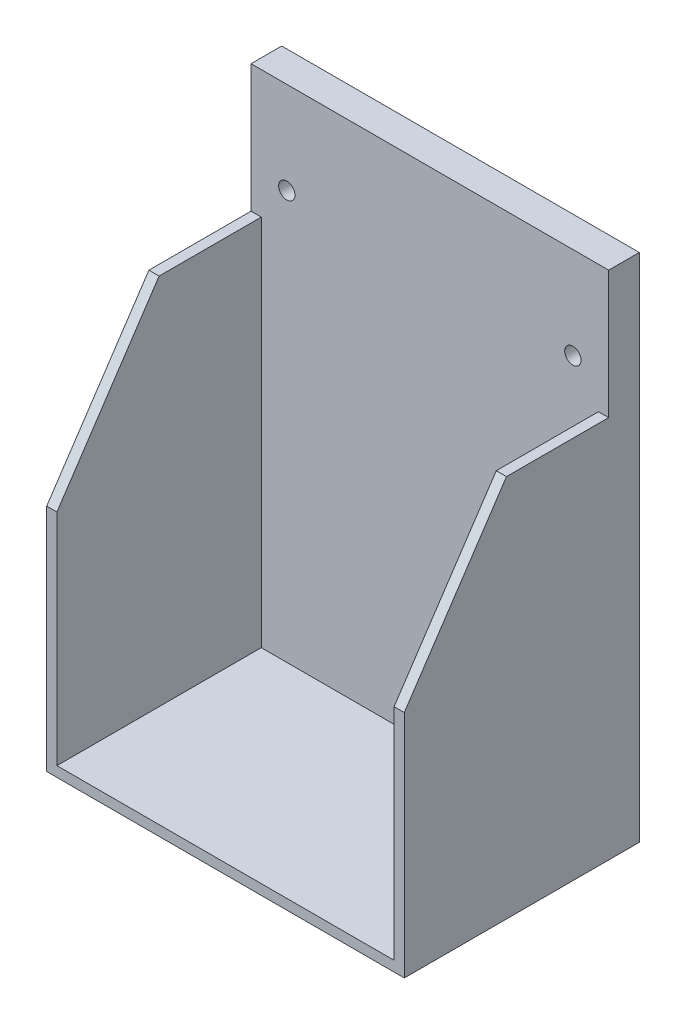
SolidWorks part; units mm, degrees
ref_plane "前视基准面" through (0, 0, 0) normal (0, 0, 1) x (1, 0, 0)
ref_plane "上视基准面" through (0, 0, 0) normal (0, 1, 0) x (1, 0, 0)
ref_plane "右视基准面" through (0, 0, 0) normal (1, 0, 0) x (0, 0, -1)
sketch "草图1" plane through (0, 0, 0) normal (0, 0, 1) x (1, 0, 0)
  line L0 (-21, -7.141) -> (49, -7.141) construction
  line L1 (-21, 17.859) -> (49, 17.859)
  line L2 (-21, 17.859) -> (-21, -82.141)
  line L3 (-21, -82.141) -> (49, -82.141)
  line L4 (49, 17.859) -> (49, -82.141)
  line L5 (-14, 17.859) -> (-14, -7.141) construction
  line L6 (-21, -0.141) -> (-14, -0.141) construction
  line L7 (14, 17.859) -> (14, -7.141) construction
  circle A0 centre (-14, -0.141) radius 1.6
  circle A1 centre (42, -0.141) radius 1.6
  dimension "D6" = 3.2
  dimension "D1" = 70
  dimension "D2" = 100
  dimension "D3" = 25
  dimension "D4" = 7
  dimension "D5" = 7
extrude "凸台-拉伸1" add sketch "草图1" along normal blind 6
sketch "草图2" plane through (0, 0, 6) normal (0, 0, 1) x (1, 0, 0)
  line L0 (-21, -82.141) -> (49, -82.141) construction
  line L1 (-21, -7.141) -> (-19, -7.141)
  line L2 (-21, -7.141) -> (-21, -82.141)
  line L3 (-21, -82.141) -> (-18.0557, -82.141)
  line L4 (-19, -7.141) -> (-19, -80.141)
  line L6 (49, -7.141) -> (47, -7.141)
  line L7 (49, -7.141) -> (49, -82.141)
  line L8 (49, -82.141) -> (46.0149, -82.141)
  line L9 (47, -7.141) -> (47, -80.141)
  line L10 (-19, -80.141) -> (47, -80.141)
  line L11 (-21, -80.141) -> (-21, -82.141)
  line L12 (-21, -82.141) -> (49, -82.141)
  line L13 (49, -79.478) -> (49, -82.141)
  point P16 (-19.8201, -82.141)
  point P17 (0, 0)
  point P18 (-18.0557, -82.141)
  point P19 (-21, -80.141)
  point P20 (0, 0)
  line M9 (-21, 17.859) -> (-21, -82.141)
  line M10 (-21, -82.141) -> (49, -82.141)
  line M11 (49, -82.141) -> (49, 17.859)
  dimension "D1" = 2
  dimension "D2" = 2
  dimension "D3" = 2
extrude "凸台-拉伸2" add sketch "草图2" along normal blind 40 contours L10 L4 L1 L2 L7 L6 L9 M9 M10 M11
sketch "草图3" plane through (-21, 0, 0) normal (-1, 0, 0) x (0, 0, 1)
  line L0 (26, -7.141) -> (46, -37.141)
  line L1 (46, -7.141) -> (6, -7.141) construction
  line L2 (46, -7.141) -> (46, -82.141) construction
  line L3 (46, -37.141) -> (46, -7.141)
  line L4 (46, -7.141) -> (26, -7.141)
  dimension "D1" = 20
  dimension "D2" = 30
extrude "切除-拉伸1" cut sketch "草图3" against normal through all
sketch "草图4" plane through (0, 0, 6) normal (0, 0, 1) x (1, 0, 0)
  line L1 (-21, -7.141) -> (49, -7.141)
  line L2 (-21, -7.141) -> (-21, -82.141)
  line L3 (-21, -82.141) -> (49, -82.141)
  line L4 (49, -7.141) -> (49, -82.141)
